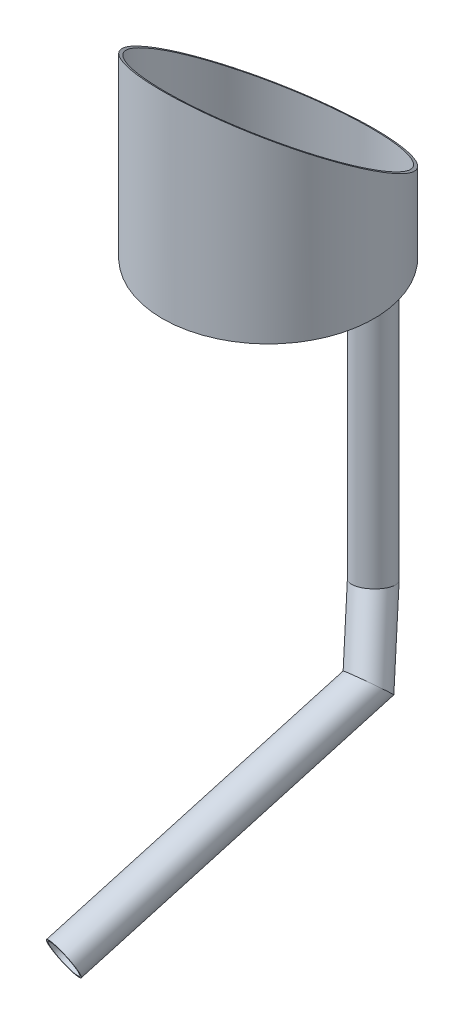
SolidWorks part; units mm, degrees
other "Markup1"
sketch "Sketch5" plane through (-150, -125, 300) normal (-0.7369, -0.649, 0.189) x (0.6573, -0.7532, -0.0234)
ref_plane "Front Plane" through (0, 0, 0) normal (0, 0, 1) x (1, 0, 0)
ref_plane "Top Plane" through (0, 0, 0) normal (0, 1, 0) x (1, 0, 0)
ref_plane "Right Plane" through (0, 0, 0) normal (1, 0, 0) x (0, 0, -1)
sketch "Sketch6" plane through (0, 0, 0) normal (0, 1, 0) x (1, 0, 0)
  line L0 (0, 0) -> (0, 117.5167) construction
  line L1 (0, 0) -> (55, 95.2628) construction
  circle A0 centre (0, 0) radius 110
  circle A1 centre (0, 0) radius 8
  circle A2 centre (40, 69.282) radius 7.5
  dimension "D1" = 220
  dimension "D2" = 16
  dimension "D4" = 15
  dimension "D3" = 80
  dimension "D5" = 30
extrude "Boss-Extrude5" add sketch "Sketch6" along normal blind 5
sketch "Sketch8" plane through (0, 5, 0) normal (0, 1, 0) x (1, 0, 0)
  circle A0 centre (0, 0) radius 110
  circle A1 centre (0, 0) radius 107
  dimension "D1" = 214
extrude "Boss-Extrude6" add sketch "Sketch8" along normal blind 200 contours A0 | A1
sketch "Sketch10" plane through (0, 0, 0) normal (1, 0, 0) x (0, 0, -1)
  line L0 (-110, 205) -> (110, 61.2865)
  line L1 (110, 0) -> (110, 205) construction
  line L2 (110, 61.2865) -> (110, 205)
  line L3 (110, 205) -> (-110, 205)
extrude "Cut-Extrude1" cut sketch "Sketch10" against normal through all both and the other way through all
sketch "Sketch11" plane through (0, 0, 0) normal (0, -1, 0) x (1, 0, 0)
  circle A0 centre (0, 0) radius 25
  circle A1 centre (0, 0) radius 17.5
  dimension "D1" = 50
  dimension "D2" = 35
extrude "Boss-Extrude7" add sketch "Sketch11" along normal blind 25
sketch "Sketch12" plane through (0, 0, 0) normal (0, -1, 0) x (1, 0, 0)
  circle A0 centre (0, 0) radius 17.5
  circle A1 centre (0, 0) radius 15
  dimension "D1" = 30
extrude "Boss-Extrude8" add sketch "Sketch12" along normal blind 14
sketch "Sketch13" plane through (0, 0, 0) normal (0, -1, 0) x (1, 0, 0)
  line L1 (43.1274, -62.3233) -> (47.4651, -62.3233)
  line L2 (43.1274, -62.3233) -> (43.1274, -65.62)
  line L3 (43.1274, -65.62) -> (47.4651, -65.62)
  line L4 (47.4651, -62.3233) -> (47.4651, -65.62)
  line L5 (43.1274, -62.3233) -> (47.4651, -65.62) construction
  line L6 (43.1274, -65.62) -> (47.4651, -62.3233) construction
  circle A0 centre (40, -69.282) radius 7.5 construction
  point P0 (45.2962, -63.9717)
extrude "Cut-Extrude2" cut sketch "Sketch13" against normal blind 10
sketch3d "3DSketch7"
  line L0 (40, 0, -69.282) -> (40, -304.8, -69.282)
  line L1 (40, 5, -69.282) -> (40, 0, -69.282) construction
  line L2 (40, -304.8, -69.282) -> (64.8193, -370.3996, -39.4973)
  line L3 (64.8193, -370.3996, -39.4973) -> (11.8914, -513.3135, 224.4672)
  line L4 (64.8193, -370.3996, -39.4973) -> (64.8193, -370.3996, 214.7171) construction
  line L5 (64.8193, -370.3996, -39.4973) -> (-196.1263, -370.3996, -39.4973) construction
  dimension "D1" = 304.8
  dimension "D2" = 76.2
  dimension "D3" = 304.8
  dimension "D4" = 30
  dimension "D5" = 80
other "Al round tubing AL RND TUBE 1.5 OD X 0.063 WALL(7)"
ref_plane "Plane1" through (40, 0, -69.282) normal (0, -1, 0) x (1, 0, 0)
sketch "Sketch1" plane through (40, 0, -69.282) normal (0, -1, 0) x (1, 0, 0)
  circle A0 centre (0, 0) radius 17.399
  circle A1 centre (0, 0) radius 19.05
  point P3 (0, 0)
  dimension "In_dia" = 34.798
  dimension "Out_dia" = 38.1
